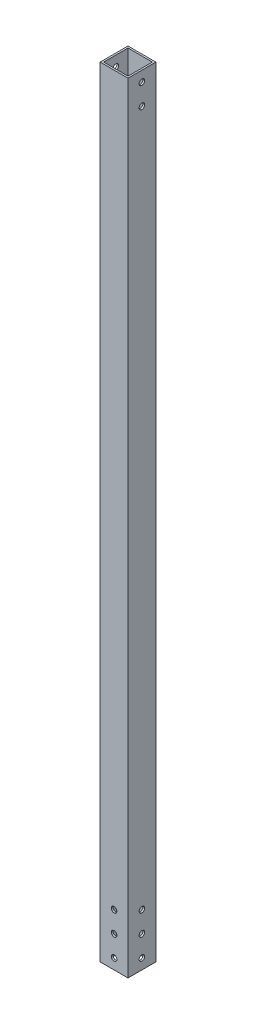
SolidWorks part; units mm, degrees
material "6061-T6 (SS)"
ref_plane "Front Plane" through (0, 0, 0) normal (0, 0, 1) x (1, 0, 0)
ref_plane "Top Plane" through (0, 0, 0) normal (0, 1, 0) x (1, 0, 0)
ref_plane "Right Plane" through (0, 0, 0) normal (1, 0, 0) x (0, 0, -1)
sketch "Sketch1" plane through (0, 0, 0) normal (0, 1, 0) x (1, 0, 0)
  line L0 (11.1125, 11.1125) -> (-11.1125, 11.1125)
  line L1 (12.7, -12.7) -> (-12.7, -12.7)
  line L2 (12.7, -12.7) -> (12.7, 12.7)
  line L3 (12.7, 12.7) -> (-12.7, 12.7)
  line L4 (-12.7, -12.7) -> (-12.7, 12.7)
  line L5 (12.7, -12.7) -> (-12.7, 12.7) construction
  line L6 (12.7, 12.7) -> (-12.7, -12.7) construction
  line L7 (-11.1125, -11.1125) -> (-11.1125, 11.1125)
  line L8 (11.1125, -11.1125) -> (-11.1125, -11.1125)
  line L9 (11.1125, -11.1125) -> (11.1125, 11.1125)
  point P0 (0, 0)
  dimension "D1" = 25.4
  dimension "D2" = 1.5875
extrude "Boss-Extrude1" add sketch "Sketch1" along normal blind 711.2
sketch "Sketch2" plane through (0, 0, 12.7) normal (0, 0, 1) x (1, 0, 0)
  line L0 (-12.7, 0) -> (12.7, 0) construction
  circle A0 centre (0, 9.525) radius 2.5527
  circle A1 centre (0, 28.575) radius 2.5527
  circle A2 centre (0, 47.625) radius 2.5527
  point P7 (0, 0)
  point P9 (0, 0)
  dimension "D1" = 9.525
  dimension "D2" = 19.05
  dimension "D3" = 5.1054
  dimension "D4" = 19.05
extrude "Cut-Extrude1" cut sketch "Sketch2" against normal through all
sketch "Sketch3" plane through (12.7, 0, 0) normal (1, 0, 0) x (0, 0, -1)
  line L0 (-12.7, 0) -> (12.7, 0) construction
  line L1 (-12.7, 711.2) -> (12.7, 711.2) construction
  circle A0 centre (0, 9.525) radius 2.5527
  circle A1 centre (0, 28.575) radius 2.5527
  circle A2 centre (0, 47.625) radius 2.5527
  circle A3 centre (0, 701.675) radius 2.5527
  circle A4 centre (0, 682.625) radius 2.5527
  point P9 (0, 0)
  dimension "D1" = 9.525
  dimension "D2" = 19.05
  dimension "D3" = 19.05
  dimension "D4" = 5.1054
  dimension "D5" = 9.525
  dimension "D6" = 19.05
extrude "Cut-Extrude2" cut sketch "Sketch3" against normal through all
